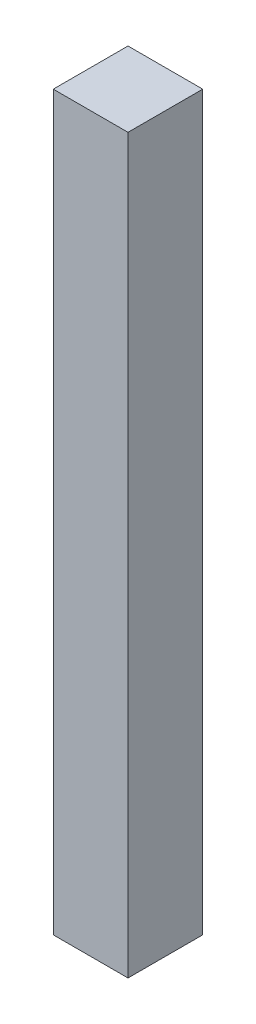
SolidWorks part; units mm, degrees
ref_plane "Plan de face" through (0, 0, 0) normal (0, 0, 1) x (1, 0, 0)
ref_plane "Plan de dessus" through (0, 0, 0) normal (0, 1, 0) x (1, 0, 0)
ref_plane "Plan de droite" through (0, 0, 0) normal (1, 0, 0) x (0, 0, -1)
sketch "Esquisse1" plane through (0, 0, 0) normal (0, 0, 1) x (1, 0, 0)
  line L1 (-50, 490) -> (50, 490)
  line L2 (-50, 490) -> (-50, -490)
  line L3 (-50, -490) -> (50, -490)
  line L4 (50, 490) -> (50, -490)
  line L5 (-50, 490) -> (50, -490) construction
  line L6 (-50, -490) -> (50, 490) construction
  point P0 (0, 0)
  dimension "D1" = 980
  dimension "D2" = 100
extrude "Boss.-Extru.1" add sketch "Esquisse1" along normal blind 100
